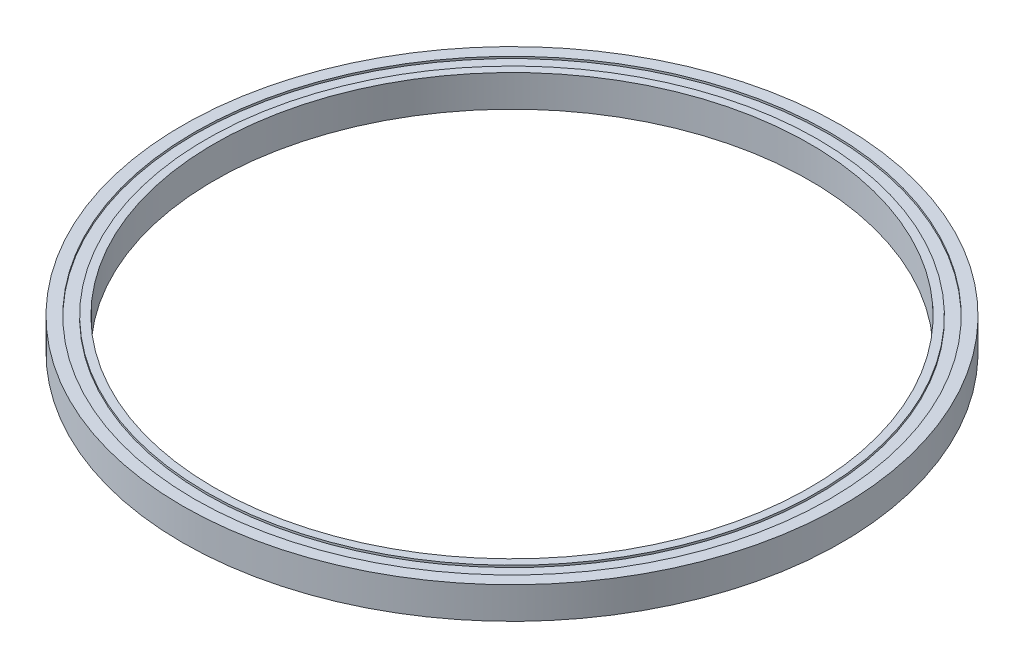
SolidWorks part; units mm, degrees
ref_plane "前视基准面" through (0, 0, 0) normal (0, 0, 1) x (1, 0, 0)
ref_plane "上视基准面" through (0, 0, 0) normal (0, 1, 0) x (1, 0, 0)
ref_plane "右视基准面" through (0, 0, 0) normal (1, 0, 0) x (0, 0, -1)
sketch "草图1" plane through (0, 0, 0) normal (0, 1, 0) x (1, 0, 0)
  circle A0 centre (0, 0) radius 75
  circle A1 centre (0, 0) radius 83
extrude "凸台-拉伸1" add sketch "草图1" along normal blind 8
sketch "草图2" plane through (0, 8, 0) normal (0, 1, 0) x (1, 0, 0)
  circle A0 centre (0, 0) radius 77
  circle A1 centre (0, 0) radius 80
extrude "切除-拉伸1" cut sketch "草图2" against normal blind 0.5
sketch "草图3" plane through (0, 0, 0) normal (0, -1, 0) x (1, 0, 0)
  circle A0 centre (0, 0) radius 77
  circle A1 centre (0, 0) radius 79.5
  circle A2 centre (0, 0) radius 75 construction
  circle A3 centre (0, 0) radius 83 construction
  dimension "D1" = 2
  dimension "D2" = 3.5
extrude "切除-拉伸2" cut sketch "草图3" against normal blind 0.5
